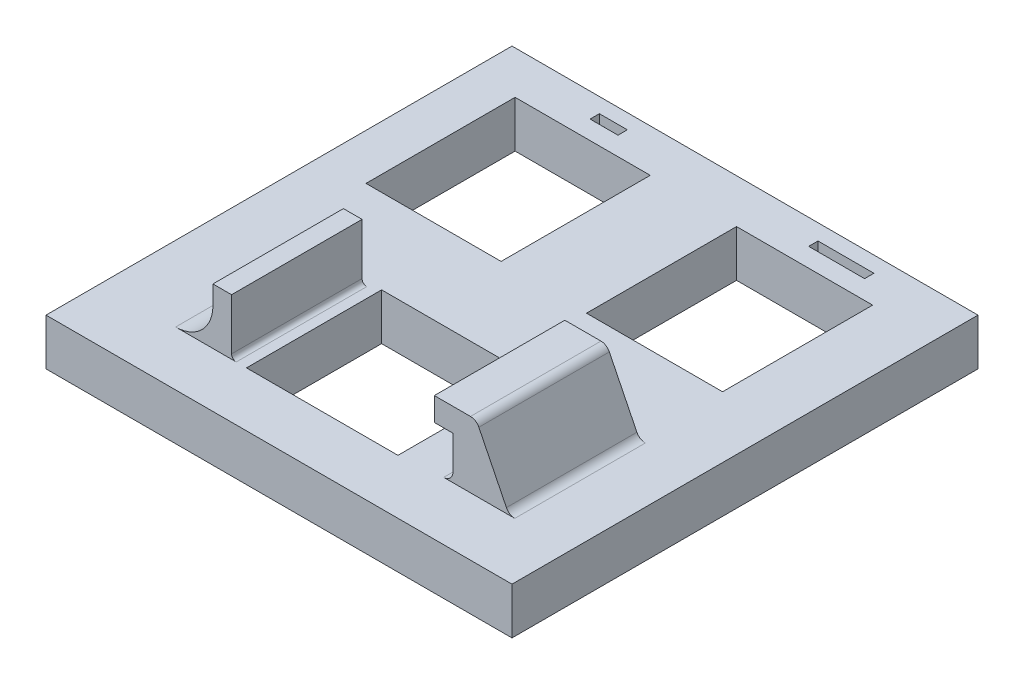
SolidWorks part; units mm, degrees
ref_plane "Front Plane" through (0, 0, 0) normal (0, 0, 1) x (1, 0, 0)
ref_plane "Top Plane" through (0, 0, 0) normal (0, 1, 0) x (1, 0, 0)
ref_plane "Right Plane" through (0, 0, 0) normal (1, 0, 0) x (0, 0, -1)
sketch "Sketch1" plane through (0, 0, 0) normal (0, 1, 0) x (1, 0, 0)
  line L1 (-25, 12.5) -> (25, 12.5)
  line L2 (-25, 12.5) -> (-25, -12.5)
  line L3 (-25, -12.5) -> (25, -12.5)
  line L4 (25, 12.5) -> (25, -12.5)
  line L5 (-25, 12.5) -> (25, -12.5) construction
  line L6 (-25, -12.5) -> (25, 12.5) construction
  point P0 (0, 0)
  dimension "D1" = 25
  dimension "D2" = 50
extrude "Boss-Extrude1" add sketch "Sketch1" along normal blind 5
sketch "Sketch2" plane through (0, 5, 0) normal (0, 1, 0) x (1, 0, 0)
  line L1 (-20.0716, 7.9037) -> (-5.5716, 7.9037)
  line L2 (-20.0716, 7.9037) -> (-20.0716, -8.0963)
  line L3 (-20.0716, -8.0963) -> (-5.5716, -8.0963)
  line L4 (-5.5716, 7.9037) -> (-5.5716, -8.0963)
  line L5 (-20.0716, 7.9037) -> (-5.5716, -8.0963) construction
  line L6 (-20.0716, -8.0963) -> (-5.5716, 7.9037) construction
  point P0 (-12.8216, -0.0963)
  dimension "D1" = 14.5
  dimension "D2" = 16
extrude "Cut-Extrude1" cut sketch "Sketch2" against normal blind 5 contours L2 L1 L4 L3
sketch "Sketch3" plane through (0, 5, 0) normal (0, 1, 0) x (1, 0, 0)
  line L1 (3.8189, 7.7737) -> (18.4189, 7.7737)
  line L2 (3.8189, 7.7737) -> (3.8189, -8.3263)
  line L3 (3.8189, -8.3263) -> (18.4189, -8.3263)
  line L4 (18.4189, 7.7737) -> (18.4189, -8.3263)
  line L5 (3.8189, 7.7737) -> (18.4189, -8.3263) construction
  line L6 (3.8189, -8.3263) -> (18.4189, 7.7737) construction
  point P0 (11.1189, -0.2763)
  dimension "D1" = 14.6
  dimension "D2" = 16.1
extrude "Cut-Extrude2" cut sketch "Sketch3" against normal blind 5
sketch "Sketch5" plane through (0, 5, 0) normal (0, 1, 0) x (1, 0, 0)
  line L1 (-14.0298, 10.9039) -> (-11.0298, 10.9039)
  line L2 (-14.0298, 10.9039) -> (-14.0298, 9.9039)
  line L3 (-14.0298, 9.9039) -> (-11.0298, 9.9039)
  line L4 (-11.0298, 10.9039) -> (-11.0298, 9.9039)
  line L5 (9.5287, 10.8029) -> (15.5287, 10.8029)
  line L6 (9.5287, 10.8029) -> (9.5287, 9.8029)
  line L7 (9.5287, 9.8029) -> (15.5287, 9.8029)
  line L8 (15.5287, 10.8029) -> (15.5287, 9.8029)
  dimension "D1" = 1
  dimension "D2" = 3
  dimension "D3" = 6
  dimension "D4" = 1
extrude "Cut-Extrude3" cut sketch "Sketch5" against normal blind 1
sketch "Sketch6" plane through (0, 0, 0) normal (0, 1, 0) x (1, 0, 0)
  line L1 (-25, -12.5) -> (25, -12.5)
  line L2 (-25, -12.5) -> (-25, -37.5)
  line L3 (-25, -37.5) -> (25, -37.5)
  line L4 (25, -12.5) -> (25, -37.5)
  dimension "D1" = 25
  dimension "D2" = 50
extrude "Boss-Extrude2" add sketch "Sketch6" along normal blind 5
sketch "Sketch7" plane through (0, 5, 0) normal (0, 1, 0) x (1, 0, 0)
  line L1 (6.9104, -17.149) -> (6.9104, -31.649)
  line L2 (6.9104, -17.149) -> (-9.3396, -17.149)
  line L3 (-9.3396, -17.149) -> (-9.3396, -31.649)
  line L4 (6.9104, -31.649) -> (-9.3396, -31.649)
  dimension "D1" = 14.5
  dimension "D2" = 16.25
extrude "Cut-Extrude4" cut sketch "Sketch7" against normal blind 4 contours L2 L1 L4 L3
sketch "Sketch8" plane through (0, 1, 0) normal (0, 1, 0) x (1, 0, 0)
  line L5 (6.9104, -17.149) -> (-9.3396, -17.149) construction
  line L6 (-9.3396, -31.649) -> (5.4104, -31.649)
  line L7 (-9.3396, -31.649) -> (-9.3396, -17.149)
  line L8 (-9.3396, -17.149) -> (5.4104, -17.149)
  line L9 (5.4104, -31.649) -> (5.4104, -17.149)
  dimension "D1" = 14.75
extrude "Cut-Extrude5" cut sketch "Sketch8" against normal blind 1
sketch "Sketch9" plane through (0, 5, 0) normal (0, 1, 0) x (1, 0, 0)
  line L5 (6.9104, -17.149) -> (6.9104, -31.649) construction
  line L6 (12.4104, -17.2424) -> (14.9104, -17.2424)
  line L7 (12.4104, -17.2424) -> (12.4104, -31.2424)
  line L8 (12.4104, -31.2424) -> (14.9104, -31.2424)
  line L9 (14.9104, -17.2424) -> (14.9104, -31.2424)
  dimension "D1" = 14
  dimension "D2" = 2.5
  dimension "D3" = 5.5
extrude "Boss-Extrude3" add sketch "Sketch9" along normal blind 4.6
sketch "Sketch10" plane through (0, 9.6, 0) normal (0, 1, 0) x (1, 0, 0)
  line L1 (14.9104, -17.2424) -> (9.9104, -17.2424)
  line L2 (14.9104, -17.2424) -> (14.9104, -31.2424)
  line L3 (14.9104, -31.2424) -> (9.9104, -31.2424)
  line L4 (9.9104, -17.2424) -> (9.9104, -31.2424)
  dimension "D1" = 14
  dimension "D2" = 5
extrude "Boss-Extrude4" add sketch "Sketch10" along normal blind 2.5
sketch "Sketch11" plane through (0, 0, 31.2424) normal (0, 0, 1) x (1, 0, 0)
  line L0 (14.9104, 5) -> (18.4189, 5)
  line L1 (18.4189, 5) -> (14.9104, 12.1)
  line L2 (14.9104, 12.1) -> (14.9104, 5)
extrude "Boss-Extrude5" add sketch "Sketch11" against normal blind 14
fillet "Fillet1" radius 1 2 edges at (18.4189, 5, 24.2424) (14.9104, 12.1, 24.2424)
sketch "Sketch12" plane through (0, 5, 0) normal (0, 1, 0) x (1, 0, 0)
  line L0 (-9.3396, -17.149) -> (-9.3396, -31.649) construction
  line L1 (-10.9396, -17.649) -> (-12.9396, -17.649)
  line L2 (-10.9396, -17.649) -> (-10.9396, -31.649)
  line L3 (-10.9396, -31.649) -> (-12.9396, -31.649)
  line L4 (-12.9396, -17.649) -> (-12.9396, -31.649)
  line L5 (6.9104, -31.649) -> (-9.3396, -31.649) construction
  dimension "D1" = 14
  dimension "D2" = 2
  dimension "D3" = 1.6
extrude "Boss-Extrude6" add sketch "Sketch12" along normal blind 6
fillet "Fillet2" radius 4 1 edges at (-12.9396, 5, 24.649)
fillet "Fillet3" radius 1 1 edges at (12.4104, 5, 24.2424)
fillet "Fillet4" radius 0.5 1 edges at (-10.9396, 5, 24.649)
sketch "Sketch13" plane through (9.9104, 0, 0) normal (-1, 0, 0) x (0, 0, 1)
  line L1 (17.2424, 12.1) -> (31.2424, 12.1)
  line L2 (17.2424, 12.1) -> (17.2424, 9.6)
  line L3 (17.2424, 9.6) -> (31.2424, 9.6)
  line L4 (31.2424, 12.1) -> (31.2424, 9.6)
extrude "Cut-Extrude6" cut sketch "Sketch13" against normal blind 0.5
